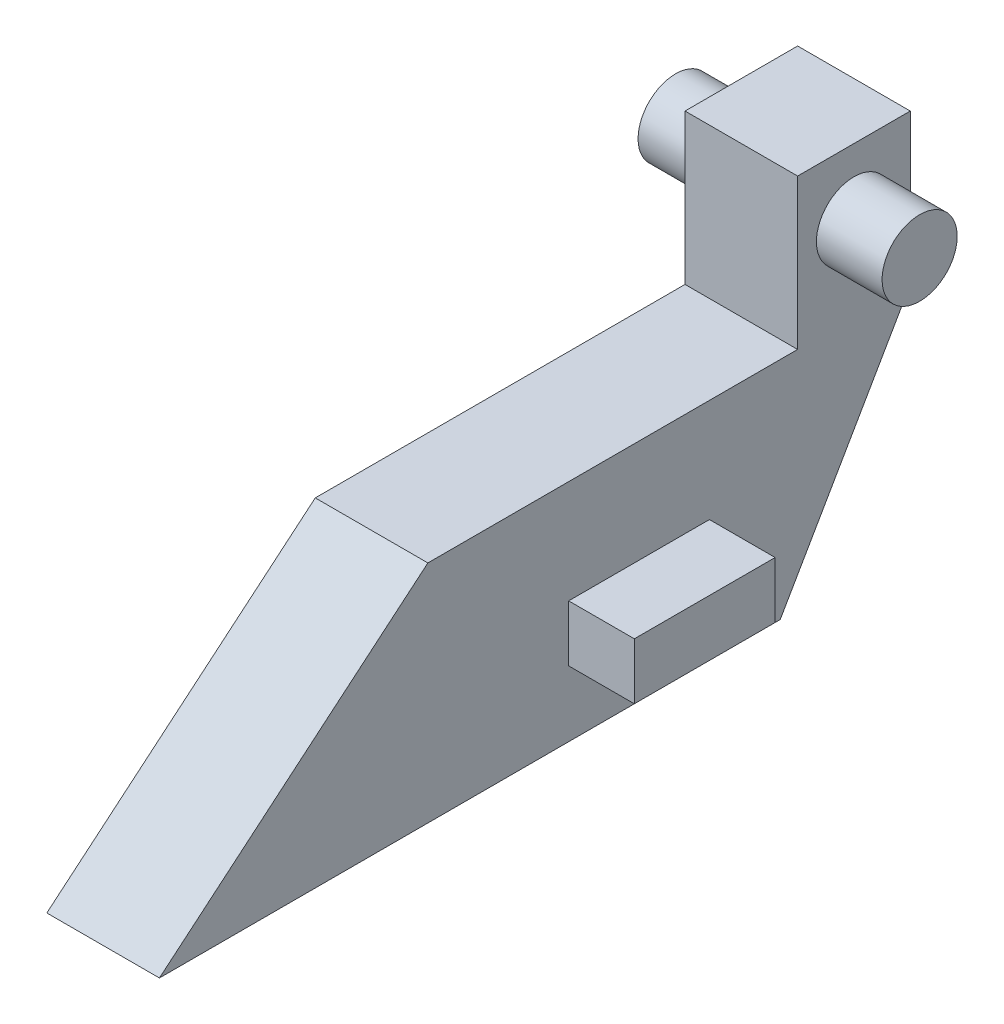
SolidWorks part; units mm, degrees
ref_plane "Front Plane" through (0, 0, 0) normal (0, 0, 1) x (1, 0, 0)
ref_plane "Top Plane" through (0, 0, 0) normal (0, 1, 0) x (1, 0, 0)
ref_plane "Right Plane" through (0, 0, 0) normal (1, 0, 0) x (0, 0, -1)
sketch "Sketch1" plane through (0, 0, 0) normal (0, 0, 1) x (1, 0, 0)
  line L1 (-6, 0) -> (6, 0)
  line L2 (-6, 0) -> (-6, 24)
  line L3 (-6, 24) -> (6, 24)
  line L4 (6, 0) -> (6, 24)
  point P5 (0, 0)
  dimension "D1" = 12
  dimension "D2" = 24
extrude "Boss-Extrude1" add sketch "Sketch1" against normal blind 80
sketch "Sketch2" plane through (6, 0, 0) normal (1, 0, 0) x (0, 0, -1)
  line L0 (0, 0) -> (28.6021, 24)
  line L5 (80, 24) -> (0, 24) construction
  line L6 (80, 0) -> (0, 0) construction
  line L7 (80, 24) -> (66.1436, 0)
  line L8 (66.1436, 0) -> (80, 0)
  line L9 (80, 0) -> (80, 24)
  line M4 (0, 24) -> (0, 0)
  line M5 (0, 0) -> (80, 0)
  line M6 (80, 0) -> (80, 24)
  line M7 (80, 24) -> (0, 24)
  dimension "D1" = 40
  dimension "D2" = 60
extrude "Cut-Extrude1" cut sketch "Sketch2" against normal up to vertex (12 mm away) contours L0 M4 M7 | L7 M6 M5
sketch "Sketch4" plane through (6, 0, 0) normal (1, 0, 0) x (0, 0, -1)
  line L0 (66.1436, 0) -> (0, 0) construction
  line L1 (43.6021, 13) -> (58.6021, 13)
  line L2 (43.6021, 13) -> (43.6021, 7)
  line L3 (43.6021, 7) -> (58.6021, 7)
  line L4 (58.6021, 13) -> (58.6021, 7)
  dimension "D1" = 15
  dimension "D2" = 6
  dimension "D3" = 15
  dimension "D4" = 7
extrude "Boss-Extrude2" add sketch "Sketch4" along normal blind 7
mirror "Mirror1" about plane through (0, 0, 0) normal (1, 0, 0) of "Boss-Extrude2"
sketch "Sketch5" plane through (0, 24, 0) normal (0, 1, 0) x (1, 0, 0)
  line L3 (6, 80) -> (6, 28.6021) construction
  line L4 (-6, 80) -> (6, 80)
  line L5 (-6, 80) -> (-6, 68)
  line L6 (-6, 68) -> (6, 68)
  line L7 (6, 80) -> (6, 68)
extrude "Boss-Extrude3" add sketch "Sketch5" along normal blind 16
sketch "Sketch7" plane through (0, 0, 0) normal (1, 0, 0) x (0, 0, -1)
  line L0 (68, 40) -> (80, 40) construction
  circle A0 centre (74, 32.938) radius 4
  point P4 (74, 40)
  dimension "D1" = 8
extrude "Boss-Extrude4" add sketch "Sketch7" along normal mid plane 26
